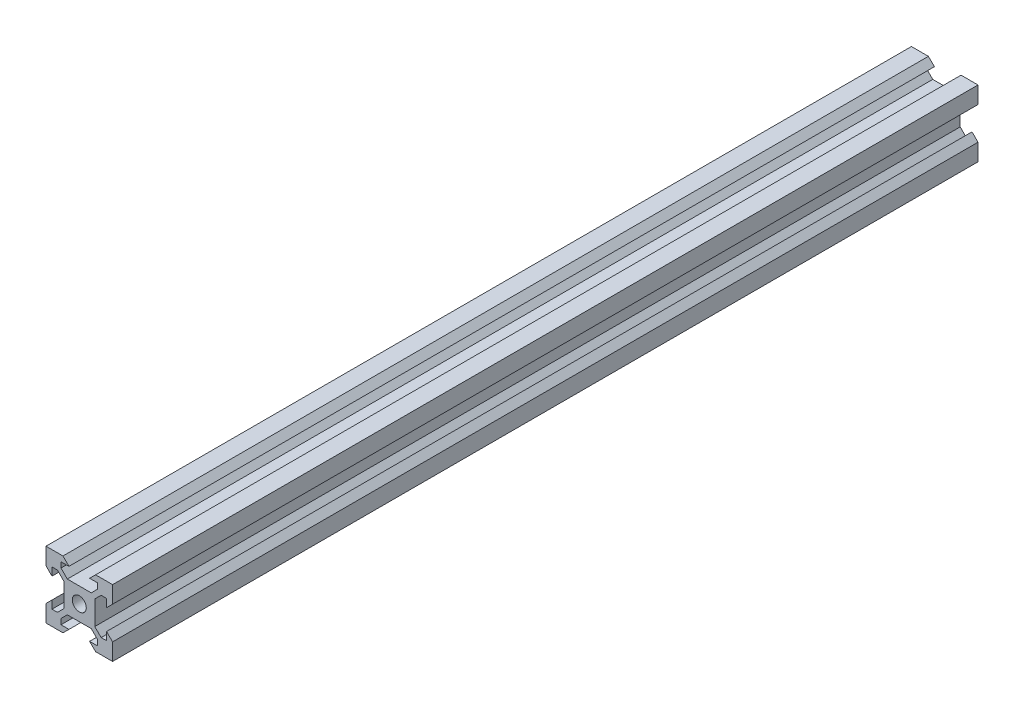
SolidWorks part; units mm, degrees
material "6063-T5"
ref_plane "Front Plane" through (0, 0, 0) normal (0, 0, 1) x (1, 0, 0)
ref_plane "Top Plane" through (0, 0, 0) normal (0, 1, 0) x (1, 0, 0)
ref_plane "Right Plane" through (0, 0, 0) normal (1, 0, 0) x (0, 0, -1)
sketch "Sketch1" plane through (0, 0, 0) normal (0, 0, 1) x (1, 0, 0)
  line L0 (3.59, 4.6507) -> (-3.59, 4.6507)
  line L5 (-10, -10) -> (10, -10)
  line L6 (-10, -10) -> (-10, 10)
  line L7 (-10, 10) -> (10, 10)
  line L8 (10, -10) -> (10, 10)
  line L9 (-10, -10) -> (10, 10) construction
  line L10 (-10, 10) -> (10, -10) construction
  line L11 (0, 10) -> (0, -10) construction
  line L12 (10, 0) -> (-10, 0) construction
  line L13 (-3.59, 4.6507) -> (-5.4993, 6.56)
  line L14 (-5.4993, 6.56) -> (-5.4993, 8.2)
  line L15 (3.59, 4.6507) -> (5.4993, 6.56)
  line L16 (5.4993, 6.56) -> (5.4993, 8.2)
  line L17 (5.4993, 8.2) -> (3.1, 8.2)
  line L18 (3.1, 8.2) -> (4.9, 10)
  line L19 (-5.4993, 8.2) -> (-3.1, 8.2)
  line L20 (-3.1, 8.2) -> (-4.9, 10)
  line L21 (3.1, -8.2) -> (4.9, -10)
  line L22 (5.4993, -8.2) -> (3.1, -8.2)
  line L23 (5.4993, -6.56) -> (5.4993, -8.2)
  line L24 (3.59, -4.6507) -> (5.4993, -6.56)
  line L25 (3.59, -4.6507) -> (-3.59, -4.6507)
  line L26 (-3.59, -4.6507) -> (-5.4993, -6.56)
  line L27 (-5.4993, -6.56) -> (-5.4993, -8.2)
  line L28 (-5.4993, -8.2) -> (-3.1, -8.2)
  line L29 (-3.1, -8.2) -> (-4.9, -10)
  line L30 (8.2, 3.1) -> (10, 4.9)
  line L31 (8.2, 3.1) -> (8.2, 5.4993)
  line L32 (8.2, 5.4993) -> (6.56, 5.4993)
  line L33 (4.6507, 3.59) -> (6.56, 5.4993)
  line L34 (4.6507, 3.59) -> (4.6507, -3.59)
  line L35 (4.6507, -3.59) -> (6.56, -5.4993)
  line L36 (8.2, -5.4993) -> (6.56, -5.4993)
  line L37 (8.2, -3.1) -> (8.2, -5.4993)
  line L38 (8.2, -3.1) -> (10, -4.9)
  line L39 (-8.2, -3.1) -> (-10, -4.9)
  line L40 (-8.2, -3.1) -> (-8.2, -5.4993)
  line L41 (-8.2, -5.4993) -> (-6.56, -5.4993)
  line L42 (-4.6507, -3.59) -> (-6.56, -5.4993)
  line L43 (-4.6507, 3.59) -> (-4.6507, -3.59)
  line L44 (-4.6507, 3.59) -> (-6.56, 5.4993)
  line L45 (-8.2, 5.4993) -> (-6.56, 5.4993)
  line L46 (-8.2, 3.1) -> (-8.2, 5.4993)
  line L47 (-8.2, 3.1) -> (-10, 4.9)
  line L48 (4.9, 10) -> (-4.9, 10)
  line L49 (-10, 4.9) -> (-10, -4.9)
  line L50 (10, -4.9) -> (10, 4.9)
  line L51 (4.9, -10) -> (-4.9, -10)
  circle A1 centre (0, 0) radius 2.1
  point P11 (0, 4.6507)
  point P35 (4.6507, 0)
  dimension "D1" = 4.2
  dimension "D2" = 20
  dimension "D3" = 20
  dimension "D4" = 0.75
  dimension "D5" = 3.59
  dimension "D6" = 3.1
  dimension "D7" = 1.8
  dimension "D8" = 1.64
  dimension "D9" = 3.59
  dimension "D10" = 1.64
  dimension "D11" = 1.8
  dimension "D12" = 45
  dimension "D13" = 0.75
  dimension "D14" = 3.1
extrude "Boss-Extrude1" add sketch "Sketch1" along normal mid plane 260 contours L6 L5 L8 L7 | A1 | L50 L30 L31 L32 L33 L34 L35 L36 L37 L38 | L48 L20 L19 L14 L13 L0 L15 L16 L17 L18 | L49 L39 L40 L41 L42 L43 L44 L45 L46 L47 | L51 L29 L28 L27 L26 L25 L24 L23 L22 L21
